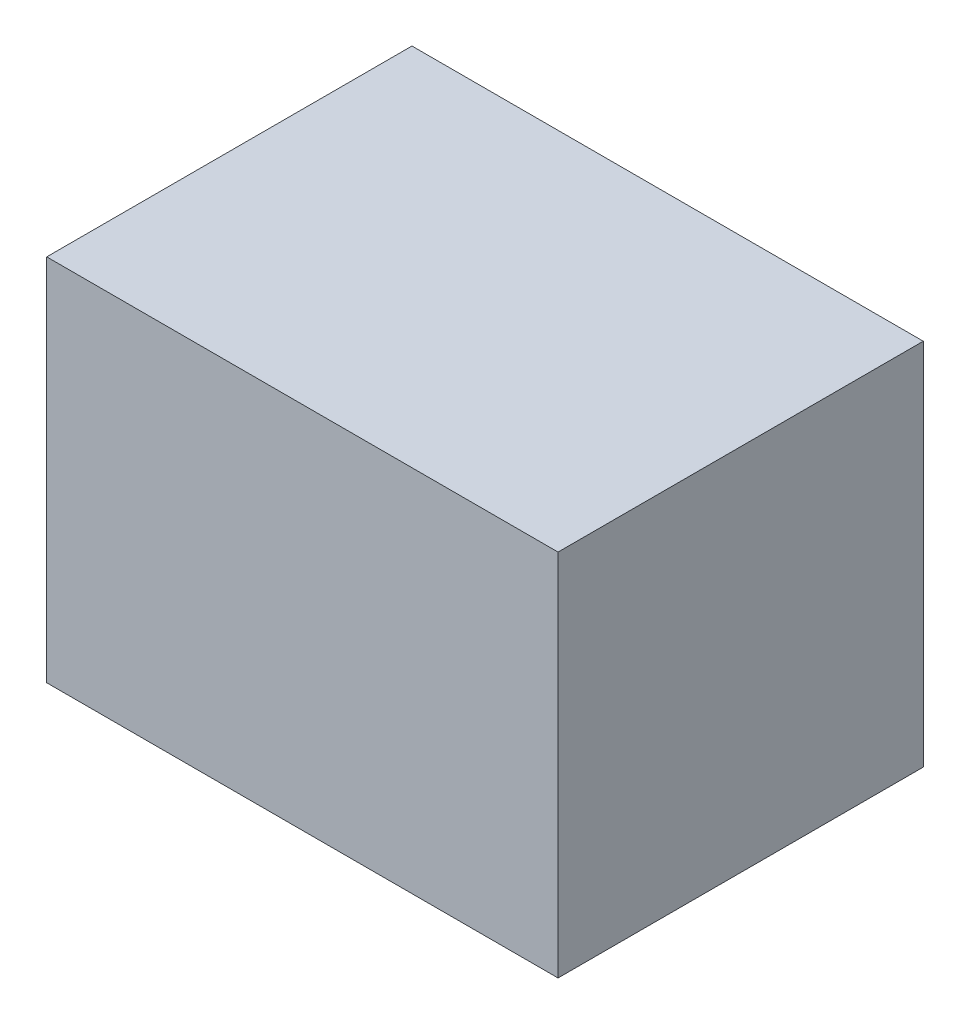
SolidWorks part; units mm, degrees
ref_plane "Front" through (0, 0, 0) normal (0, 0, 1) x (1, 0, 0)
ref_plane "Top" through (0, 0, 0) normal (0, 1, 0) x (1, 0, 0)
ref_plane "Right" through (0, 0, 0) normal (1, 0, 0) x (0, 0, -1)
sketch "Sketch1" plane through (0, 0, 0) normal (0, 0, 1) x (1, 0, 0)
  line L1 (-70, 50) -> (70, 50)
  line L2 (-70, 50) -> (-70, -50)
  line L3 (-70, -50) -> (70, -50)
  line L4 (70, 50) -> (70, -50)
  line L5 (-70, 50) -> (70, -50) construction
  line L6 (-70, -50) -> (70, 50) construction
  point P0 (0, 0)
  dimension "D1" = 140
  dimension "D2" = 100
extrude "Boss-Extrude1" add sketch "Sketch1" along normal blind 100
shell "Shell1" thickness 1
sketch "Sketch2" plane through (0, 50, 0) normal (0, 1, 0) x (1, 0, 0)
  line L5 (-70, 0) -> (70, 0)
  line L6 (-70, 0) -> (-70, -100)
  line L7 (-70, -100) -> (70, -100)
  line L8 (70, 0) -> (70, -100)
extrude "Boss-Extrude2" add sketch "Sketch2" along normal blind 1
